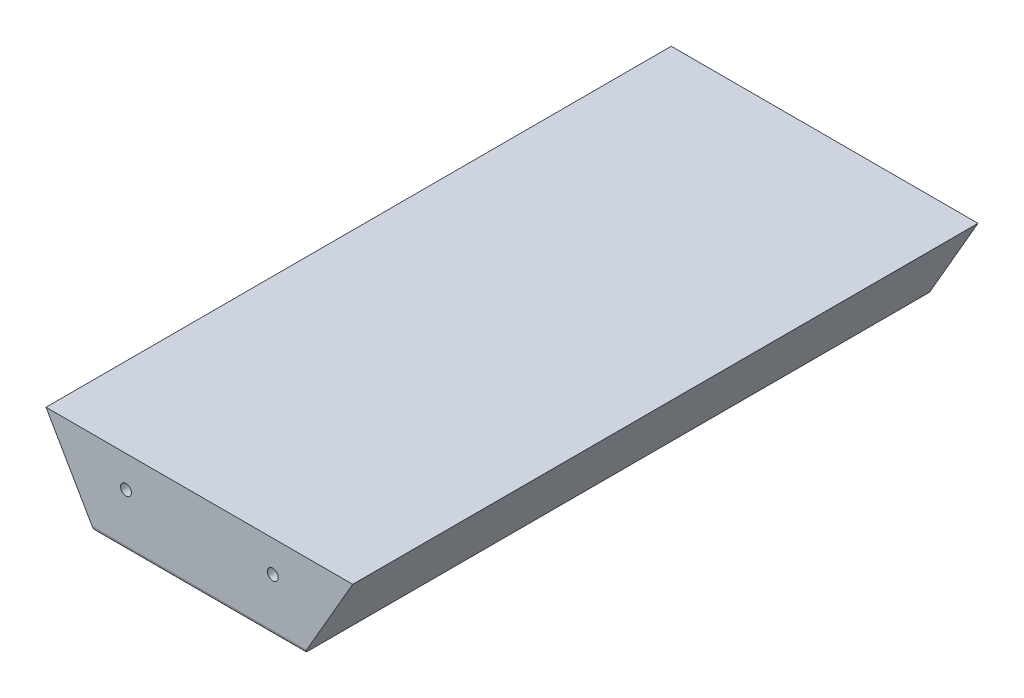
SolidWorks part; units mm, degrees
ref_plane "Front Plane" through (0, 0, 0) normal (0, 0, 1) x (1, 0, 0)
ref_plane "Top Plane" through (0, 0, 0) normal (0, 1, 0) x (1, 0, 0)
ref_plane "Right Plane" through (0, 0, 0) normal (1, 0, 0) x (0, 0, -1)
sketch "Sketch1" plane through (0, 0, 0) normal (0, 0, 1) x (1, 0, 0)
  line L0 (50, 0) -> (-50, 0)
  line L1 (-50, 0) -> (-73.094, 40)
  line L2 (-73.094, 40) -> (73.094, 40)
  line L3 (73.094, 40) -> (50, 0)
  point P4 (0, 0)
  dimension "D1" = 120
  dimension "D2" = 120
  dimension "D3" = 100
  dimension "D4" = 40
extrude "Boss-Extrude1" add sketch "Sketch1" along normal mid plane 200
sketch "Sketch3" plane through (0, 0, 0) normal (0, -1, 0) x (1, 0, 0)
  line L0 (0, 100) -> (0, -100) construction
  line L1 (-50, 100) -> (50, 100) construction
  line L2 (-50, -100) -> (50, -100) construction
  circle A0 centre (0, 70) radius 5
  circle A2 centre (0, -70) radius 5
  circle A3 centre (0, 0) radius 5
  dimension "D1" = 10
  dimension "D3" = 30
  dimension "D4" = 70
  dimension "D5" = 10
  dimension "D6" = 10
  dimension "D2" = 30
extrude "Cut-Extrude2" cut sketch "Sketch3" against normal blind 15
sketch "Sketch9" plane through (0, 0, -100) normal (0, 0, -1) x (-1, 0, 0)
  line L0 (50, 0) -> (-50, 0) construction
  line L1 (50, 0) -> (-50, 0)
  line L2 (73.094, 40) -> (50, 0) construction
  line L3 (73.094, 40) -> (50, 0)
  line L4 (-73.094, 40) -> (73.094, 40) construction
  line L5 (-73.094, 40) -> (73.094, 40)
  line L6 (-50, 0) -> (-73.094, 40) construction
  line L7 (-50, 0) -> (-73.094, 40)
sketch "Sketch10" plane through (0, 0, 100) normal (0, 0, 1) x (1, 0, 0)
  line L0 (-50, 0) -> (50, 0)
  line L1 (50, 0) -> (73.094, 40)
  line L2 (73.094, 40) -> (-73.094, 40)
  line L3 (-73.094, 40) -> (-50, 0)
extrude "Boss-Extrude5" add sketch "Sketch9" along normal blind 50
extrude "Boss-Extrude6" add sketch "Sketch10" along normal blind 48
fillet "Fillet1" radius 1.8 1 edges at (0, 0, 148)
sketch "Sketch11" plane through (0, 0, 148) normal (0, 0, 1) x (1, 0, 0)
  line L0 (0, 0) -> (0, 25) construction
  line L1 (0, 25) -> (-35, 25) construction
  line L2 (50, 0) -> (-50, 0) construction
  circle A0 centre (-35, 25) radius 2.6
  circle A1 centre (35, 25) radius 2.6
  dimension "D1" = 35
  dimension "D3" = 5.2
  dimension "D2" = 25
extrude "Cut-Extrude3" cut sketch "Sketch11" against normal blind 15
sketch "Sketch12" plane through (0, 0, -150) normal (0, 0, -1) x (-1, 0, 0)
  circle A0 centre (-35, 25) radius 2.6 construction
  circle A1 centre (-35, 25) radius 2.6
  circle A2 centre (35, 25) radius 2.6 construction
  circle A3 centre (35, 25) radius 2.6
extrude "Cut-Extrude4" cut sketch "Sketch12" against normal blind 15
